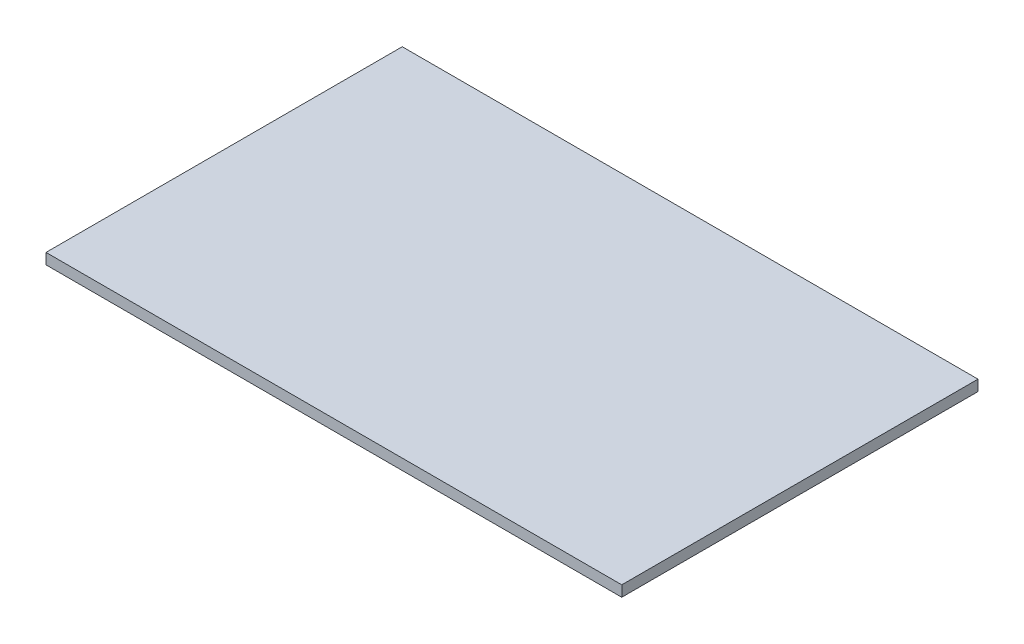
SolidWorks part; units mm, degrees
ref_plane "Front Plane" through (0, 0, 0) normal (0, 0, 1) x (1, 0, 0)
ref_plane "Top Plane" through (0, 0, 0) normal (0, 1, 0) x (1, 0, 0)
ref_plane "Right Plane" through (0, 0, 0) normal (1, 0, 0) x (0, 0, -1)
sketch "Sketch1" plane through (0, 0, 0) normal (0, 1, 0) x (1, 0, 0)
  line L1 (0, 0) -> (160, 0)
  line L2 (0, 0) -> (0, 99)
  line L3 (0, 99) -> (160, 99)
  line L4 (160, 0) -> (160, 99)
  line L5 (0, 0) -> (160, 99) construction
  line L6 (0, 99) -> (160, 0) construction
  point P4 (80, 49.5)
  dimension "D1" = 160
  dimension "D2" = 99
extrude "Boss-Extrude1" add sketch "Sketch1" along normal blind 3
